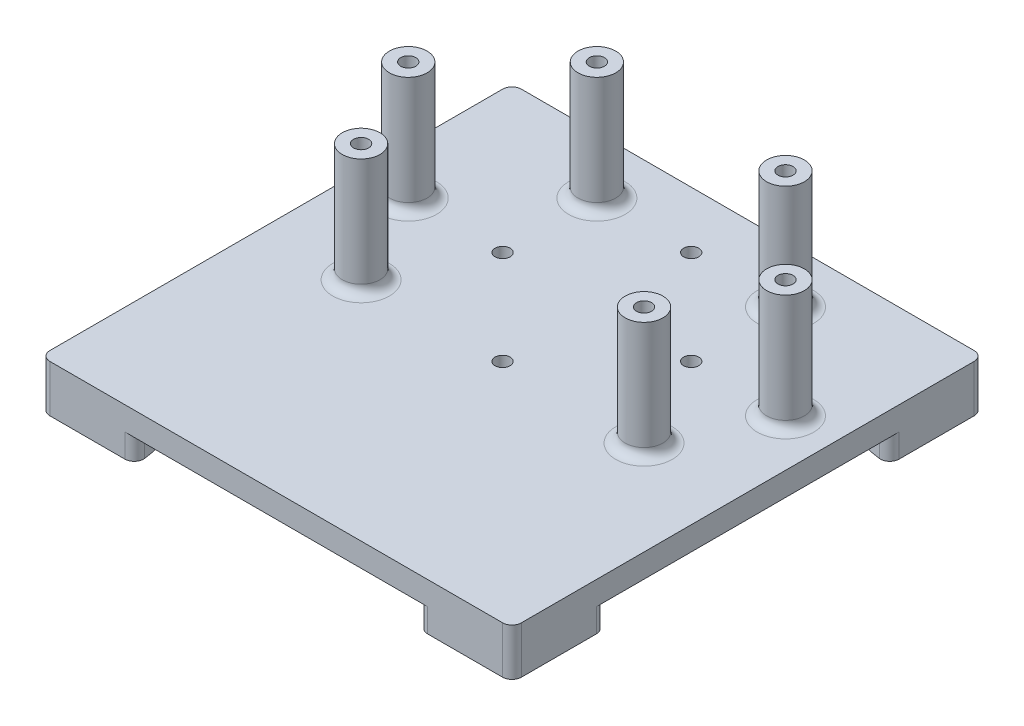
SolidWorks part; units mm, degrees
ref_plane "前视基准面" through (0, 0, 0) normal (0, 0, 1) x (1, 0, 0)
ref_plane "上视基准面" through (0, 0, 0) normal (0, 1, 0) x (1, 0, 0)
ref_plane "右视基准面" through (0, 0, 0) normal (1, 0, 0) x (0, 0, -1)
sketch "草图1" plane through (57, 0, 0) normal (0, 1, 0) x (1, 0, 0)
  line L1 (-50, -50) -> (50, -50)
  line L2 (-50, -50) -> (-50, 50)
  line L3 (-50, 50) -> (50, 50)
  line L4 (50, -50) -> (50, 50)
  line L5 (-50, -50) -> (50, 50) construction
  line L6 (-50, 50) -> (50, -50) construction
  point P0 (0, 0)
  dimension "D1" = 100
  dimension "D2" = 100
extrude "凸台-拉伸1" add sketch "草图1" along normal blind 5
sketch "草图5" plane through (0, 5, 0) normal (0, 1, 0) x (1, 0, 0)
  line L0 (107, 50) -> (7, 50) construction
  line L1 (107, -50) -> (107, 50) construction
  line L2 (57, 50) -> (57, -65.041) construction
  circle A0 centre (77, 38) radius 1.6
  circle A1 centre (97, 18) radius 1.6
  circle A2 centre (87, -2) radius 1.6
  circle A3 centre (77, 38) radius 4
  circle A4 centre (97, 18) radius 4
  circle A5 centre (87, -2) radius 4
  circle A6 centre (27, -2) radius 4
  circle A7 centre (27, -2) radius 1.6
  circle A8 centre (17, 18) radius 4
  circle A9 centre (17, 18) radius 1.6
  circle A10 centre (37, 38) radius 4
  circle A11 centre (37, 38) radius 1.6
  dimension "D1" = 3.2
  dimension "D5" = 32
  dimension "D8" = 8
  dimension "D9" = 8
  dimension "D10" = 8
  dimension "D2" = 12
  dimension "D3" = 30
  dimension "D4" = 10
  dimension "D6" = 52
  dimension "D7" = 20
extrude "凸台-拉伸2" add sketch "草图5" along normal blind 25
sketch "草图6" plane through (0, 5, 0) normal (0, 1, 0) x (1, 0, 0)
  line L0 (107, 50) -> (7, 50) construction
  line L1 (107, -50) -> (107, 50) construction
  line L2 (7, 50) -> (7, -50) construction
  circle A1 centre (57, 38) radius 1.6
  circle A2 centre (37, 18) radius 1.6
  circle A3 centre (77, 18) radius 1.6
  circle A4 centre (57, -2) radius 1.6
  dimension "D1" = 12
  dimension "D2" = 3.2
  dimension "D3" = 50
  dimension "D4" = 30
  dimension "D5" = 32
  dimension "D6" = 32
  dimension "D7" = 30
  dimension "D8" = 52
  dimension "D9" = 50
extrude "切除-拉伸1" cut sketch "草图6" against normal up to surface (5 mm away) up to face at (57, 0, 0)
sketch "草图7" plane through (0, 0, 0) normal (0, -1, 0) x (1, 0, 0)
  line L0 (57, 50) -> (57, -50) construction
  line L1 (7, 50) -> (27, 50)
  line L2 (7, 50) -> (7, 30)
  line L4 (107, -50) -> (107, 50)
  line L5 (107, 50) -> (7, 50)
  line L6 (7, 50) -> (7, -50)
  line L7 (7, -50) -> (107, -50)
  line L8 (107, -50) -> (107, 50)
  line L9 (107, 50) -> (7, 50)
  line L10 (7, 50) -> (7, -50)
  line L11 (7, -50) -> (107, -50)
  line L13 (7, 0) -> (106.606, 0) construction
  line L16 (107, 50) -> (107, 30)
  line L17 (107, 50) -> (87, 50)
  line L18 (107, -50) -> (107, -30)
  line L21 (107, -50) -> (87, -50)
  line L24 (7, -50) -> (27, -50)
  line L25 (7, -50) -> (7, -30)
  arc A0 (87, -50) -> (107, -30) centre (107, -50) cw
  arc A1 (7, -30) -> (27, -50) centre (7, -50) cw
  arc A2 (27, 50) -> (7, 30) centre (7, 50) cw
  arc A3 (87, 50) -> (107, 30) centre (107, 50) ccw
  line M9 (107, -50) -> (107, 50)
  line M10 (107, 50) -> (7, 50)
  line M11 (7, 50) -> (7, -50)
  line M12 (7, -50) -> (107, -50)
  dimension "D2" = 20
  dimension "D1" = 0
extrude "凸台-拉伸3" add sketch "草图7" along normal blind 5 contours A2 M10 M11 | A1 L10 M12 | A0 L11 M9 | L16 A3 L17
fillet "圆角1" radius 2 18 edges at (107, -2.5, 30) (87, -2.5, 50) (27, -2.5, 50) (7, -2.5, 30) (7, -2.5, -30) (27, -2.5, -50) (87, -2.5, -50) (107, -2.5, -30) (7, 0, 50) (7, 0, -50) (27, 5, -2) (17, 5, -22) (37, 5, -42) (77, 5, -42) (97, 5, -22) (87, 5, -2) (107, 0, 50) (107, 0, -50)
